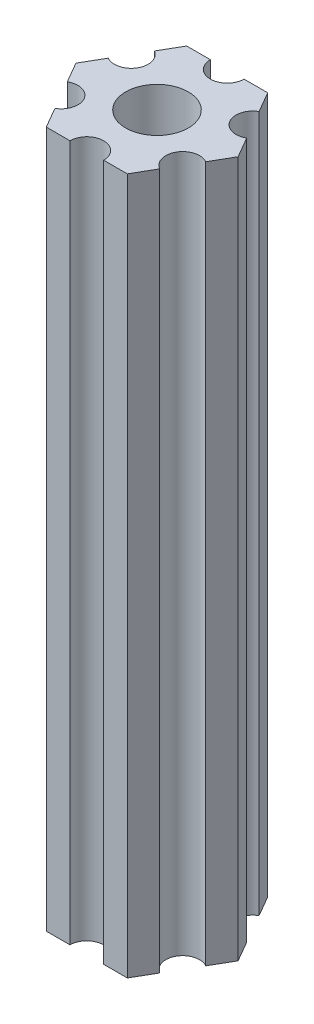
SolidWorks part; units mm, degrees
material "Churro - 6005A-T61"
ref_plane "Plano frontal" through (0, 0, 0) normal (0, 0, 1) x (1, 0, 0)
ref_plane "Plano superior" through (0, 0, 0) normal (0, 1, 0) x (1, 0, 0)
ref_plane "Plano direito" through (0, 0, 0) normal (1, 0, 0) x (0, 0, -1)
ref_plane "Plano1" through (0, 85, 0) normal (0, 1, 0) x (1, 0, 0)
sketch "Esboço1" plane through (0, 85, 0) normal (0, 1, 0) x (1, 0, 0)
  line L0 (6.1627, -1.826) -> (7.2169, 0)
  line L1 (7.2169, 0) -> (6.1627, 1.826)
  line L2 (4.6627, 4.424) -> (3.6084, 6.25)
  line L3 (3.6084, 6.25) -> (1.5, 6.25)
  line L4 (-1.5, 6.25) -> (-3.6084, 6.25)
  line L5 (-3.6084, 6.25) -> (-4.6627, 4.424)
  line L6 (-6.1627, 1.826) -> (-7.2169, 0)
  line L7 (-7.2169, 0) -> (-6.1627, -1.826)
  line L8 (-4.6627, -4.424) -> (-3.6084, -6.25)
  line L9 (-3.6084, -6.25) -> (-1.5, -6.25)
  line L10 (1.5, -6.25) -> (3.6084, -6.25)
  line L11 (3.6084, -6.25) -> (4.6627, -4.424)
  arc A0 (6.1627, 1.826) -> (4.6627, 4.424) centre (5.4127, 3.125) cw
  arc A1 (1.5, 6.25) -> (-1.5, 6.25) centre (0, 6.25) cw
  arc A2 (-4.6627, 4.424) -> (-6.1627, 1.826) centre (-5.4127, 3.125) cw
  arc A3 (-6.1627, -1.826) -> (-4.6627, -4.424) centre (-5.4127, -3.125) cw
  arc A4 (-1.5, -6.25) -> (1.5, -6.25) centre (0, -6.25) cw
  arc A5 (4.6627, -4.424) -> (6.1627, -1.826) centre (5.4127, -3.125) cw
  circle A6 centre (0, 0) radius 2.79
extrude "Ressalto-extrusão1" add sketch "Esboço1" against normal blind 62
